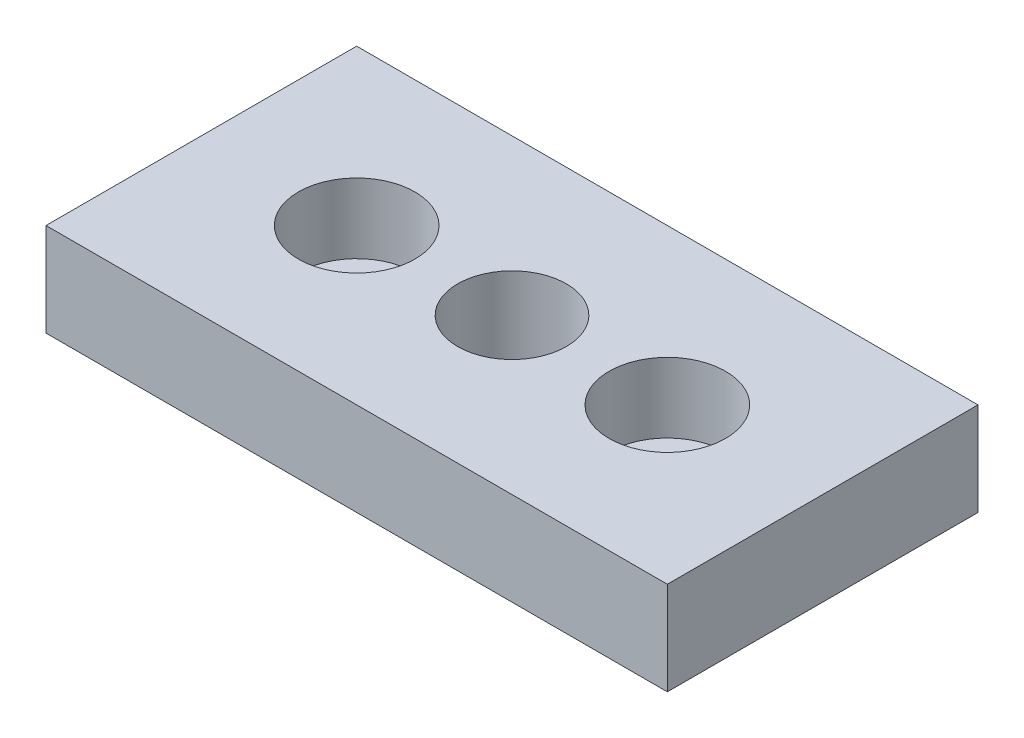
SolidWorks part; units mm, degrees
material "Алюминиевый сплав"
ref_plane "Спереди" through (0, 0, 0) normal (0, 0, 1) x (1, 0, 0)
ref_plane "Сверху" through (0, 0, 0) normal (0, 1, 0) x (1, 0, 0)
ref_plane "Справа" through (0, 0, 0) normal (1, 0, 0) x (0, 0, -1)
sketch "Эскиз1" plane through (0, 0, 0) normal (0, 1, 0) x (1, 0, 0)
  line L1 (-40, -20) -> (40, -20)
  line L2 (-40, -20) -> (-40, 20)
  line L3 (-40, 20) -> (40, 20)
  line L4 (40, -20) -> (40, 20)
  line L5 (-40, -20) -> (40, 20) construction
  line L6 (-40, 20) -> (40, -20) construction
  point P0 (0, 0)
  dimension "D1" = 80
  dimension "D2" = 40
extrude "Бобышка-Вытянуть1" add sketch "Эскиз1" along normal blind 12
sketch "Эскиз2" plane through (0, 0, 0) normal (0, 0, 1) x (1, 0, 0)
  line L0 (0, 0) -> (0, 12) construction
  line L1 (-40, 0) -> (40, 0) construction
  line L2 (-40, 12) -> (40, 12) construction
  line L3 (-27.5, 12) -> (-27.5, 3)
  line L4 (-27.5, 3) -> (-24.5, 3)
  line L5 (-24.5, 3) -> (-24.5, 0)
  line L6 (-24.5, 0) -> (-20, 0)
  line L7 (-20, 0) -> (-20, 12) construction
  line L8 (-20, 12) -> (-27.5, 12)
  line L9 (-20, 12) -> (-20, 0)
  dimension "D1" = 9
  dimension "D2" = 3
  dimension "D3" = 15
  dimension "D4" = 40
revolve "Вырез-Повернуть1" cut sketch "Эскиз2" angle 360 about L9
mirror "Зеркальное отражение1" about plane through (0, 0, 0) normal (1, 0, 0) of "Вырез-Повернуть1"
hole_wizard "Отверстие обработанное метчиком M161" positions "Эскиз6" profile "Эскиз7" tap size "M16" standard "ISO" end condition up to next
sketch "Эскиз6" plane through (0, 12, 0) normal (0, 1, 0) x (1, 0, 0)
  point P0 (0, 0)
sketch "Эскиз7" plane through (0, 12, 0) normal (1, 0, 0) x (0, 0, 1)
  line L0 (0, 0) -> (0, 12)
  line L1 (0, 12) -> (7, 12)
  line L2 (7, 12) -> (7, 0)
  line L5 (7, 0) -> (0, 0)
  line L11 (0, -6.35) -> (0, 107.95) construction
  dimension "Диаметр проходного сверла" = 14
  dimension "Глубина проходного сверла" = 12
cosmetic thread "Отверстие резьбы2" parameters "D2"=16
